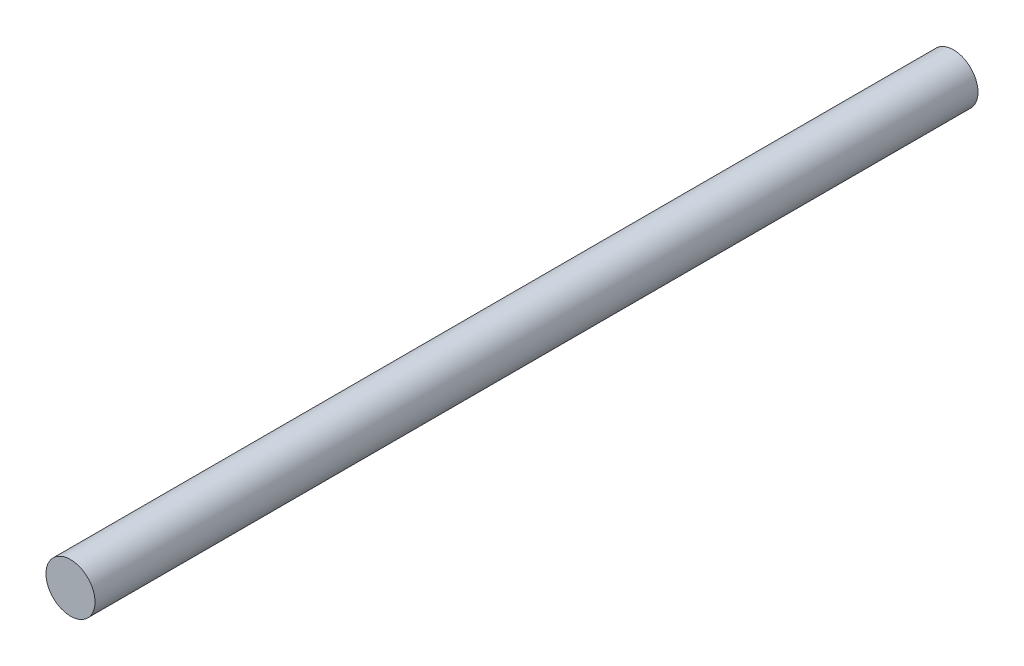
SolidWorks part; units mm, degrees
ref_plane "Piano frontale" through (0, 0, 0) normal (0, 0, 1) x (1, 0, 0)
ref_plane "Piano superiore" through (0, 0, 0) normal (0, 1, 0) x (1, 0, 0)
ref_plane "Piano destro" through (0, 0, 0) normal (1, 0, 0) x (0, 0, -1)
sketch "Schizzo1" plane through (0, 0, 0) normal (0, 0, 1) x (1, 0, 0)
  circle A0 centre (0, 0) radius 1.25
  dimension "D1" = 2.5
extrude "Estrusione-Estrusione1" add sketch "Schizzo1" along normal blind 45
